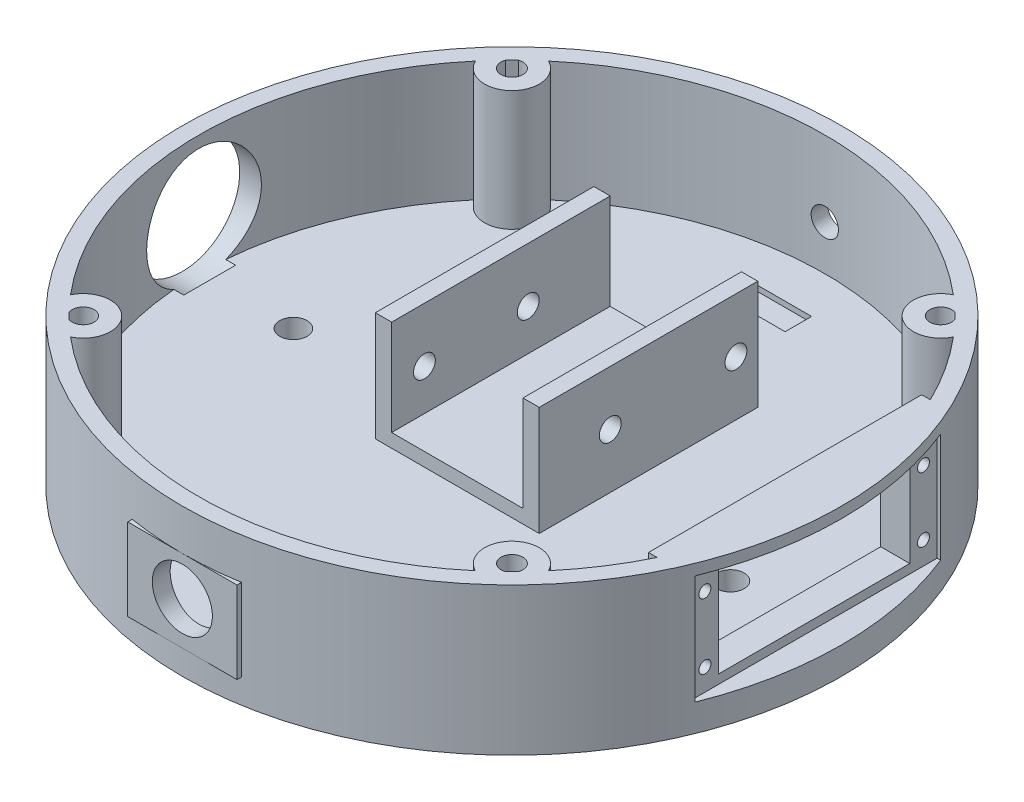
SolidWorks part; units mm, degrees
ref_plane "Front Plane" through (0, 0, 0) normal (0, 0, 1) x (1, 0, 0)
ref_plane "Top Plane" through (0, 0, 0) normal (0, 1, 0) x (1, 0, 0)
ref_plane "Right Plane" through (0, 0, 0) normal (1, 0, 0) x (0, 0, -1)
sketch "Sketch1" plane through (0, 0, 0) normal (0, 1, 0) x (1, 0, 0)
  circle A0 centre (0, 0) radius 60.325
  dimension "D1" = 120.65
extrude "Boss-Extrude1" add sketch "Sketch1" along normal blind 5
sketch "Sketch2" plane through (0, 5, 0) normal (0, 1, 0) x (1, 0, 0)
  line L9 (-15, -10) -> (15, -10)
  line L10 (-15, -10) -> (-15, 30)
  line L11 (-15, 30) -> (15, 30)
  line L12 (15, -10) -> (15, 30)
  line L13 (-15, -10) -> (15, 30) construction
  line L14 (-15, 30) -> (15, -10) construction
  point P0 (0.3114, 20.4789)
  point P5 (0, 10)
  dimension "D1" = 30
  dimension "D2" = 40
  dimension "D3" = 10
  dimension "D4" = 0
extrude "Boss-Extrude2" add sketch "Sketch2" along normal blind 20
sketch "Sketch3" plane through (0, 5, 0) normal (0, 1, 0) x (1, 0, 0)
  circle A0 centre (0, 0) radius 60.325
  circle A1 centre (0, 0) radius 57.325
  dimension "D1" = 114.65
  dimension "D2" = 3
extrude "Boss-Extrude3" add sketch "Sketch3" along normal blind 22
sketch "Sketch5" plane through (0, 5, 0) normal (0, 1, 0) x (1, 0, 0)
  line L0 (0, 0) -> (-39.2444, 39.2444)
  line L1 (0, 0) -> (39.2444, 39.2444)
  line L2 (0, 0) -> (-39.2444, -39.2444)
  line L3 (0, 0) -> (39.2444, -39.2444)
  circle A0 centre (-39.2444, 39.2444) radius 2
  circle A1 centre (-39.2444, 39.2444) radius 5
  circle A2 centre (39.2444, 39.2444) radius 2
  circle A3 centre (39.2444, 39.2444) radius 5
  circle A4 centre (-39.2444, -39.2444) radius 2
  circle A5 centre (-39.2444, -39.2444) radius 5
  circle A6 centre (39.2444, -39.2444) radius 2
  circle A7 centre (39.2444, -39.2444) radius 5
  circle A8 centre (0, 0) radius 60.325 construction
  circle M19 centre (0, 0) radius 57.325
  dimension "D1" = 4
  dimension "D2" = 10
  dimension "D3" = 4
  dimension "D4" = 10
  dimension "D5" = 10
  dimension "D6" = 4
  dimension "D7" = 4
  dimension "D8" = 10
  dimension "D9" = 55.5
  dimension "D10" = 55.5
  dimension "D11" = 55.5
  dimension "D12" = 55.5
ref_plane "Plane1" through (0, 0, 60.325) normal (0, 0, 1) x (1, 0, 0)
sketch "Sketch6" plane through (0, 0, 60.325) normal (0, 0, 1) x (1, 0, 0)
  line L1 (-10, 19.5) -> (10, 19.5)
  line L2 (-10, 19.5) -> (-10, 4.5)
  line L3 (-10, 4.5) -> (10, 4.5)
  line L4 (10, 19.5) -> (10, 4.5)
  line L5 (-10, 19.5) -> (10, 4.5) construction
  line L6 (-10, 4.5) -> (10, 19.5) construction
  point P0 (0, 12)
  dimension "D1" = 12
  dimension "D2" = 15
  dimension "D3" = 20
extrude "Boss-Extrude13" add sketch "Sketch6" against normal blind 2
sketch "Sketch7" plane through (0, 0, 60.325) normal (0, 0, 1) x (1, 0, 0)
  circle A0 centre (0, 12.3134) radius 5.5
  dimension "D1" = 11
extrude "Cut-Extrude1" cut sketch "Sketch7" against normal blind 5
sketch "Sketch8" plane through (0, 0, 10) normal (0, 0, 1) x (1, 0, 0)
  line L0 (-15, 5) -> (15, 5) construction
  line L1 (-12.0184, 27.5) -> (12.0184, 27.5)
  line L2 (-12.0184, 27.5) -> (-12.0184, 7.5)
  line L3 (-12.0184, 7.5) -> (12.0184, 7.5)
  line L4 (12.0184, 27.5) -> (12.0184, 7.5)
  line L5 (-12.0184, 27.5) -> (12.0184, 7.5) construction
  line L6 (-12.0184, 7.5) -> (12.0184, 27.5) construction
  point P0 (0, 17.5)
  dimension "D1" = 12.5
  dimension "D2" = 20
extrude "Cut-Extrude2" cut sketch "Sketch8" against normal blind 50
sketch "Sketch11" plane through (-15, 0, 0) normal (-1, 0, 0) x (0, 0, 1)
  line L0 (-30, 5) -> (10, 5) construction
  line L1 (-30, 25) -> (-30, 5) construction
  circle A0 centre (-15, 15) radius 2
  circle A1 centre (4, 15) radius 2
  dimension "D2" = 4
  dimension "D3" = 4
  dimension "D1" = 19
  dimension "D4" = 10
  dimension "D5" = 15
extrude "Cut-Extrude5" cut sketch "Sketch11" against normal blind 20
sketch "Sketch12" plane through (15, 0, 0) normal (1, 0, 0) x (0, 0, -1)
  line L0 (-10, 25) -> (-10, 5) construction
  line L1 (-10, 5) -> (30, 5) construction
  circle A0 centre (3, 15) radius 2
  circle A1 centre (26, 15) radius 2
  dimension "D3" = 4
  dimension "D4" = 4
  dimension "D1" = 23
  dimension "D2" = 13
  dimension "D5" = 10
extrude "Cut-Extrude6" cut sketch "Sketch12" against normal blind 20
ref_plane "Plane2" through (0, 0, -60.325) normal (0, 0, -1) x (-1, 0, 0)
sketch "Sketch14" plane through (0, 0, -60.325) normal (0, 0, -1) x (-1, 0, 0)
  circle A0 centre (0, 13.2159) radius 2.5
  dimension "D1" = 5
extrude "Cut-Extrude7" cut sketch "Sketch14" against normal blind 5
ref_plane "Plane3" through (-60.325, 0, 0) normal (-1, 0, 0) x (0, 0, 1)
sketch "Sketch15" plane through (-60.325, 0, 0) normal (-1, 0, 0) x (0, 0, 1)
  circle A1 centre (0, 14.0795) radius 12.5
  dimension "D1" = 25
extrude "Boss-Extrude15" add sketch "Sketch15" against normal blind 3
sketch "Sketch16" plane through (-60.325, 0, 0) normal (-1, 0, 0) x (0, 0, 1)
  circle A0 centre (0, 14.3674) radius 10.5
  dimension "D1" = 21
extrude "Cut-Extrude9" cut sketch "Sketch16" against normal blind 5
sketch "Sketch17" plane through (0, 5, 0) normal (0, 1, 0) x (1, 0, 0)
  circle A0 centre (0, 40) radius 2.5
  circle A1 centre (40, 0) radius 2.5
  circle A2 centre (0, -40) radius 2.5
  circle A3 centre (-40, 0) radius 2.5
  dimension "D5" = 5
  dimension "D6" = 5
  dimension "D7" = 5
  dimension "D8" = 5
  dimension "D1" = 40
  dimension "D2" = 40
  dimension "D3" = 40
  dimension "D4" = 40
extrude "Cut-Extrude10" cut sketch "Sketch17" against normal blind 5
ref_plane "Plane4" through (60.325, 0, 0) normal (1, 0, 0) x (0, 0, -1)
sketch "Sketch20" plane through (0, 5, 0) normal (0, 1, 0) x (1, 0, 0)
  line L1 (-5.1053, 49.3333) -> (5.5119, 49.3333)
  line L2 (-5.1053, 49.3333) -> (-5.1053, 44.4903)
  line L3 (-5.1053, 44.4903) -> (5.5119, 44.4903)
  line L4 (5.5119, 49.3333) -> (5.5119, 44.4903)
  line L5 (-5.1053, 49.3333) -> (5.5119, 44.4903) construction
  line L6 (-5.1053, 44.4903) -> (5.5119, 49.3333) construction
  point P0 (0.2033, 46.9118)
extrude "Cut-Extrude13" cut sketch "Sketch20" against normal blind 1
ref_plane "Plane6" through (50, 0, 0) normal (1, 0, 0) x (0, 0, -1)
sketch "Sketch26" plane through (50, 0, 0) normal (1, 0, 0) x (0, 0, -1)
  line L1 (-25, 5) -> (25, 5)
  line L2 (-25, 5) -> (-25, 27)
  line L3 (-25, 27) -> (25, 27)
  line L4 (25, 5) -> (25, 27)
  line L5 (-25, 5) -> (25, 27) construction
  line L6 (-25, 27) -> (25, 5) construction
  point P0 (0, 16)
  dimension "D1" = 0
  dimension "D2" = 16
  dimension "D3" = 22
  dimension "D4" = 50
extrude "Boss-Extrude46" add sketch "Sketch26" along normal blind 10
sketch "Sketch27" plane through (60.325, 0, 0) normal (1, 0, 0) x (0, 0, -1)
  line L1 (-22.5, 5) -> (22.5, 5)
  line L2 (-22.5, 5) -> (-22.5, 25)
  line L3 (-22.5, 25) -> (22.5, 25)
  line L4 (22.5, 5) -> (22.5, 25)
  line L5 (-22.5, 5) -> (22.5, 25) construction
  line L6 (-22.5, 25) -> (22.5, 5) construction
  point P0 (0, 15)
  dimension "D1" = 45
  dimension "D2" = 20
  dimension "D3" = 0
  dimension "D4" = 15
extrude "Cut-Extrude15" cut sketch "Sketch27" against normal blind 5
sketch "Sketch28" plane through (60.325, 0, 0) normal (1, 0, 0) x (0, 0, -1)
  line L1 (-17.5, 23.3481) -> (17.5, 23.3481)
  line L2 (-17.5, 23.3481) -> (-17.5, 6.6519)
  line L3 (-17.5, 6.6519) -> (17.5, 6.6519)
  line L4 (17.5, 23.3481) -> (17.5, 6.6519)
  line L5 (-17.5, 23.3481) -> (17.5, 6.6519) construction
  line L6 (-17.5, 6.6519) -> (17.5, 23.3481) construction
  point P0 (0, 15)
  dimension "D1" = 35
  dimension "D2" = 15
  dimension "D3" = 0
sketch "Sketch29" plane through (55.325, 0, 0) normal (1, 0, 0) x (0, 0, -1)
  circle A0 centre (-20, 21) radius 1.1
  circle A1 centre (-20, 9) radius 1.1
  circle A2 centre (20, 21) radius 1.1
  circle A3 centre (20, 9.1519) radius 1.1
  point P10 (0, 0)
  dimension "D1" = 2.2
  dimension "D2" = 2.2
  dimension "D3" = 2.2
  dimension "D4" = 2.2
  dimension "D5" = 40
  dimension "D6" = 12
  dimension "D7" = 9
extrude "Cut-Extrude17" cut sketch "Sketch29" against normal blind 10
extrude "Cut-Extrude18" cut sketch "Sketch28" against normal blind 20
sketch "Sketch30" plane through (0, 27, 0) normal (0, 1, 0) x (1, 0, 0)
  line L0 (51.7831, 30.9453) -> (68.4097, 30.9453)
  line L1 (50.8846, -32.4016) -> (67.7321, -32.4016)
  arc A0 (50.8846, -32.4016) -> (51.7831, 30.9453) centre (0, 0) ccw
  arc A1 (67.7321, -32.4016) -> (68.4097, 30.9453) centre (0, 0) ccw
  dimension "D1" = 120.65
extrude "Boss-Extrude47" add sketch "Sketch5" along normal blind 22 contours L0 A1 A0 M19 | A1 L0 A0 M19 | A5 L2 A4 M19 | L2 A5 A4 M19 | A7 L3 A6 M19 | L3 A7 A6 M19 | L1 A3 A2 M19 | A3 L1 A2 M19
extrude "Cut-Extrude19" cut sketch "Sketch30" against normal blind 30
